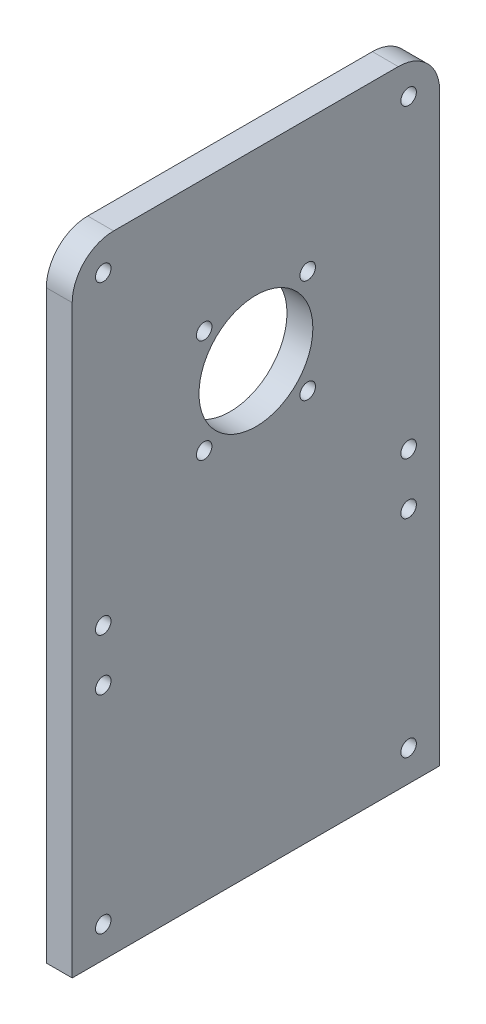
SolidWorks part; units mm, degrees
ref_plane "Front Plane" through (0, 0, 0) normal (0, 0, 1) x (1, 0, 0)
ref_plane "Top Plane" through (0, 0, 0) normal (0, 1, 0) x (1, 0, 0)
ref_plane "Right Plane" through (0, 0, 0) normal (1, 0, 0) x (0, 0, -1)
sketch "Sketch1" plane through (0, 0, 0) normal (1, 0, 0) x (0, 0, -1)
  line L1 (0, 0) -> (71, 0)
  line L2 (0, 0) -> (0, 121)
  line L3 (0, 121) -> (71, 121)
  line L4 (71, 0) -> (71, 121)
  circle A0 centre (6, 115) radius 1.5
  circle A1 centre (65, 115) radius 1.5
  circle A2 centre (35.5, 85.5) radius 11
  circle A3 centre (25.5, 95.5) radius 1.5
  circle A4 centre (45.5, 95.5) radius 1.5
  circle A5 centre (45.5, 75.5) radius 1.5
  circle A6 centre (25.5, 75.5) radius 1.5
  circle A7 centre (6, 56) radius 1.5
  circle A8 centre (65, 56) radius 1.5
  circle A9 centre (6, 6) radius 1.5
  circle A10 centre (65, 6) radius 1.5
  circle A11 centre (6, 46) radius 1.5
  circle A12 centre (65, 46) radius 1.5
  dimension "D3" = 3
  dimension "D7" = 22
  dimension "D14" = 3
  dimension "D17" = 3
  dimension "D18" = 10
  dimension "D1" = 71
  dimension "D2" = 121
  dimension "D4" = 6
  dimension "D5" = 6
  dimension "D6" = 6
  dimension "D8" = 35.5
  dimension "D9" = 35.5
  dimension "D10" = 20
  dimension "D11" = 10
  dimension "D12" = 10
  dimension "D13" = 20
  dimension "D15" = 59
  dimension "D16" = 6
extrude "Boss-Extrude1" add sketch "Sketch1" along normal blind 5
fillet "Fillet1" radius 8 2 edges at (2.5, 121, -71) (2.5, 121, 0)
